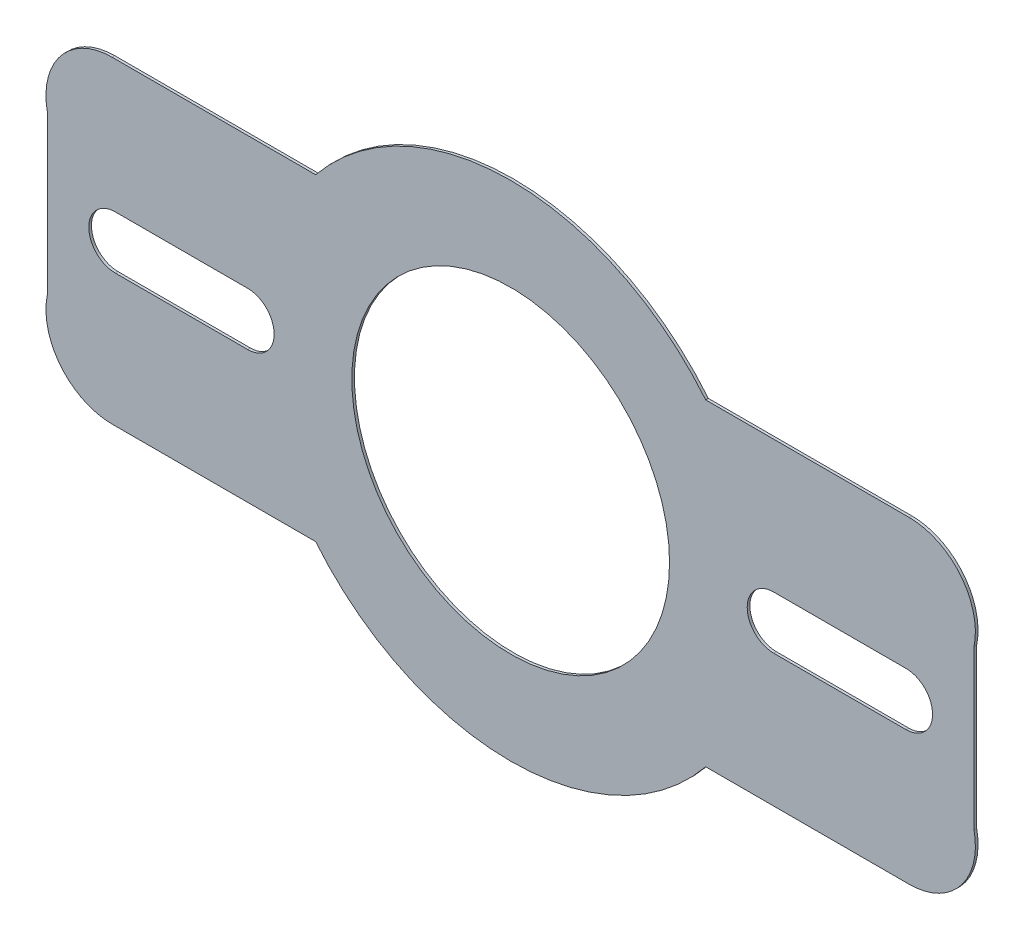
SolidWorks part; units mm, degrees
ref_plane "Front Plane" through (0, 0, 0) normal (0, 0, 1) x (1, 0, 0)
ref_plane "Top Plane" through (0, 0, 0) normal (0, 1, 0) x (1, 0, 0)
ref_plane "Right Plane" through (0, 0, 0) normal (1, 0, 0) x (0, 0, -1)
sketch "Sketch1" plane through (0, 0, 0) normal (0, 0, 1) x (1, 0, 0)
  line L0 (-73.6546, 0) -> (-175, 0) construction
  line L1 (0, 60) -> (-73.6546, 60) construction
  line L2 (-73.6546, 60) -> (-73.6546, -60) construction
  line L3 (-73.6546, -60) -> (0, -60) construction
  line L4 (0, 178.4763) -> (0, -213.7376) construction
  line L5 (-73.6546, 60) -> (-150.5051, 60)
  line L7 (-73.6546, -60) -> (-150.5051, -60)
  line L8 (-175, 30) -> (-175, -30)
  line L9 (-149.3273, 10) -> (-99.3273, 10)
  line L11 (-149.3273, -10) -> (-99.3273, -10)
  line L17 (73.6546, 0) -> (175, 0) construction
  line L18 (149.3273, -10) -> (99.3273, -10)
  line L19 (149.3273, 10) -> (99.3273, 10)
  line L20 (73.6546, 60) -> (150.5051, 60)
  line L21 (175, 30) -> (175, -30)
  line L22 (73.6546, -60) -> (150.5051, -60)
  circle A0 centre (0, 0) radius 60
  arc A1 (-73.6546, -60) -> (73.6546, -60) centre (0, 0) ccw
  arc A4 (-149.3273, 10) -> (-149.3273, -10) centre (-149.3273, 0) ccw
  arc A5 (-99.3273, 10) -> (-99.3273, -10) centre (-99.3273, 0) cw
  arc A6 (-150.5051, 60) -> (-175, 30) centre (-150.5051, 35) ccw
  arc A7 (-150.5051, -60) -> (-175, -30) centre (-150.5051, -35) cw
  arc A8 (73.6546, 60) -> (-73.6546, 60) centre (0, 0) ccw
  arc A9 (99.3273, 10) -> (99.3273, -10) centre (99.3273, 0) ccw
  arc A10 (149.3273, 10) -> (149.3273, -10) centre (149.3273, 0) cw
  arc A11 (150.5051, 60) -> (175, 30) centre (150.5051, 35) cw
  arc A12 (150.5051, -60) -> (175, -30) centre (150.5051, -35) ccw
  point P23 (0, 0)
  dimension "D1" = 120
  dimension "D2" = 95
  dimension "D7" = 25
  dimension "D3" = 120
  dimension "D4" = 20
  dimension "D5" = 50
  dimension "D6" = 175
extrude "Boss-Extrude1" add sketch "Sketch1" along normal blind 1
